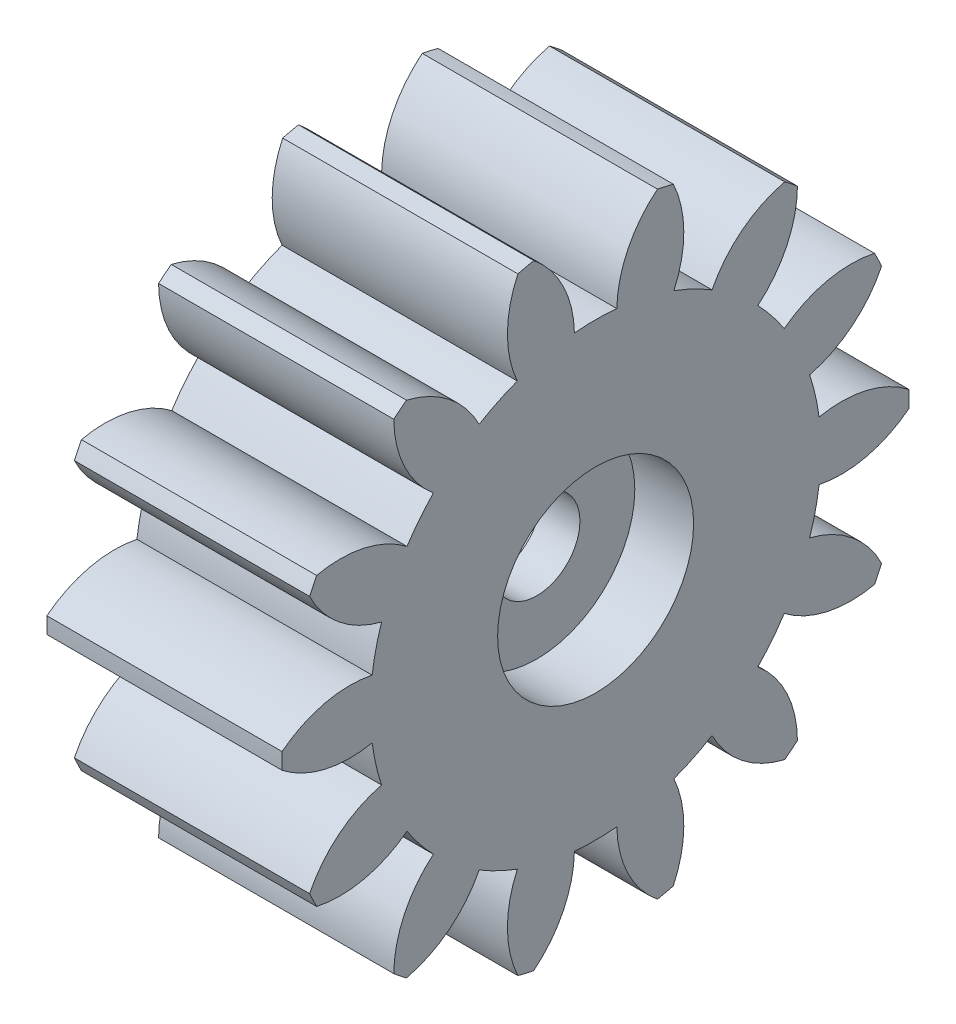
SolidWorks part; units mm, degrees
ref_plane "Plane1" through (0, 0, 0) normal (0, 0, 1) x (1, 0, 0)
ref_plane "Plane2" through (0, 0, 0) normal (0, 1, 0) x (1, 0, 0)
ref_plane "Plane3" through (0, 0, 0) normal (1, 0, 0) x (0, 0, -1)
other "Configuration Table"
sketch "HoldingSke" plane through (0, 0, 0) normal (0, 1, 0) x (1, 0, 0)
  line L0 (0, 0) -> (0.9703, -0.2419)
  line L1 (-15, 0) -> (100, 0) construction
  line L2 (0, 0) -> (-2.1039, 2.3779)
  line L3 (0, 0) -> (-11.863, 4.5341)
  line L4 (0, 0) -> (8.3795, 2.0892)
  line L5 (0, 0) -> (-46.8476, -17.4728)
  line L6 (0, 0) -> (-4.9738, -3.3558)
  line L7 (-2.1039, 2.3779) -> (8.6586, 51.2059)
  line L8 (-76.2, 54.61) -> (-75.3, 54.61)
  line L9 (-71.009, 38.7566) -> (-53.1078, 45.2721)
  line L10 (-76.2, 71.12) -> (104.1128, 71.12)
  line L11 (0, 0) -> (-6, 0)
  line L12 (-76.2, 101.6) -> (-76.162, 101.6)
  line L13 (24.9733, 27.94) -> (52.9518, 28.4284)
  line L14 (24.9733, 27.94) -> (24.9743, 27.94)
  line L15 (24.9733, 27.94) -> (100.4006, 29.5858)
  line L16 (-63.627, -1) -> (-12.827, -1)
  circle A0 centre (0, 0) radius 2.5
  circle A1 centre (0, 0) radius 5.749
  circle A2 centre (0, 0) radius 37.5
  circle A3 centre (0, 0) radius 2.5
  dimension "MHD" = 11.498
  dimension "Hub_dia" = 75
  dimension "Bore" = 5
  dimension "MBD" = 5
  dimension "Num_teeth" = 14
  dimension "Pitch" = 1
  dimension "Overall_len" = 50
  dimension "Show_teeth" = 14
  dimension "Thickness" = 6
  dimension "OAL" = 50.0001
  dimension "T_dim" = 0.9
  dimension "Ap" = 20
  dimension "H" = 19.05
  dimension "Pitch_radius" = 180.3128
  dimension "Width" = 6
  dimension "Backlash" = 0.038
  dimension "Addendum_fac" = 1
  dimension "Dedendum_fac" = 1.25
  dimension "Clearance_fac" = 0.25
  dimension "Dedendum_add" = 0.001
  dimension "Module" = 1
sketch "BasProSke" plane through (0, 0, 0) normal (0, 1, 0) x (1, 0, 0)
  line L0 (-10, 0) -> (60, 0) construction
  line L1 (0, 0) -> (0, 8)
  line L2 (0, 0) -> (6, 0)
  line L3 (6, 0) -> (6, 8)
  line L4 (6, 8) -> (0, 8)
  dimension "Thickness" = 6
  dimension "Diameter" = 16
revolve "Base-Revolve" add sketch "BasProSke" angle 360 about L0
sketch "TooCutSke" plane through (0, 0, 0) normal (1, 0, 0) x (0, 0, -1)
  line L1 (0, 0) -> (0, 107) construction
  line L2 (0, 0) -> (-0.8502, 6.9482) construction
  line L3 (0, 0) -> (-3.0989, 13.5772) construction
  line L4 (-0.8502, 6.9482) -> (-1.5494, 6.7886) construction
  arc A0 (0.5404, 5.7235) -> (-0.5404, 5.7235) centre (0, 0) ccw
  arc A1 (1.6036, 7.8636) -> (-1.6036, 7.8636) centre (0, 0) ccw
  circle A2 centre (0, 0) radius 7 construction
  circle A3 centre (0, 0) radius 6.5778 construction
  arc A4 (-0.5404, 5.7235) -> (-1.6036, 7.8636) centre (-3.3398, 5.6669) ccw
  arc A5 (1.6036, 7.8636) -> (0.5404, 5.7235) centre (3.3398, 5.6669) ccw
  dimension "Root_dia" = 11.498
  dimension "Overcut_dia" = 16.0508
  dimension "Pitch_dia" = 14
  dimension "Base_dia" = 13.1557
  dimension "Flank_rad" = 2.8
  dimension "Half_ang" = 12.857
  dimension "Half_CT" = 0.7173
extrude "ToothCut" cut sketch "TooCutSke" along normal through all
fillet "Breaks" [suppressed] radius 0.02
fillet "RootFillets" [suppressed] radius 0.251
pattern_circular "TeethCuts" count 14 every 25.714 about axis through (-10, 0, 0) along (1, 0, 0) of "ToothCut", "RootFillets", "Breaks"
sketch "HubNeaOneSke" plane through (0, 0, 0) normal (-1, 0, 0) x (0, 0, 1)
  circle A0 centre (0, 0) radius 5.749
  dimension "Diameter" = 11.498
extrude "HubNearOne" [suppressed] add sketch "HubNeaOneSke" along normal blind 44.0001
sketch "HubNeaBotSke" plane through (0, 0, 0) normal (-1, 0, 0) x (0, 0, 1)
  circle A0 centre (0, 0) radius 5.749
  dimension "Diameter" = 11.498
extrude "HubNearBoth" [suppressed] add sketch "HubNeaBotSke" along normal blind 22
ref_plane "FarPln" through (6, 0, 0) normal (1, 0, 0) x (0, 0, -1)
sketch "HubFarSke" plane through (6, 0, 0) normal (1, 0, 0) x (0, 0, -1)
  circle A0 centre (0, 0) radius 5.749
  dimension "Diameter" = 11.498
extrude "HubFar" [suppressed] add sketch "HubFarSke" along normal blind 22
sketch "BorSke" plane through (0, 0, 0) normal (1, 0, 0) x (0, 0, -1)
  circle A0 centre (0, 0) radius 2.5
  dimension "Diameter" = 5
extrude "Bore" cut sketch "BorSke" along normal mid plane 100.0001
sketch "KeySke" plane through (0, 0, 0) normal (1, 0, 0) x (0, 0, -1)
  line L0 (-1, 0) -> (-1, 3.4)
  line L1 (-1, 3.4) -> (1, 3.4)
  line L2 (1, 3.4) -> (1, 0)
  line L3 (0, 0) -> (0, 34) construction
  line L4 (-1, 0) -> (1, 0)
  dimension "Offset" = 3.4
  dimension "Width" = 2
extrude "Keyway" [suppressed] cut sketch "KeySke" along normal mid plane 100.0001
pattern_circular "Keyway2" [suppressed] count 2 every 90 about axis through (-10, 0, 0) along (1, 0, 0)
sketch "Sketch1" plane through (6, 0, 0) normal (1, 0, 0) x (0, 0, -1)
  circle A0 centre (0, 0) radius 2.5
  circle A1 centre (0, 0) radius 2.5 construction
extrude "Boss-Extrude1" add sketch "Sketch1" against normal blind 2.5
sketch "Sketch2" plane through (6, 0, 0) normal (1, 0, 0) x (0, 0, -1)
  circle A0 centre (0, 0) radius 2.5
  circle A1 centre (0, 0) radius 2.5 construction
extrude "Cut-Extrude1" cut sketch "Sketch2" against normal blind 1.5
sketch "Sketch3" plane through (4.5, 0, 0) normal (1, 0, 0) x (0, 0, -1)
  circle A0 centre (0, 0) radius 1.1
  dimension "D1" = 2.2
extrude "Cut-Extrude2" cut sketch "Sketch3" against normal through all
equation "' \"Module@HoldingSke\" = 6.35"
equation "' \"Num_teeth@HoldingSke\" = 12"
equation "' \"Ap@HoldingSke\" =  20"
equation "' \"Ap@HoldingSke\" = 20"
equation "' \"Width@HoldingSke\" = 0.5 * 25.4"
equation "' \"Hub_dia@HoldingSke\"= 1 * 25.4"
equation "' \"Hub_dia@HoldingSke\" = 1 * 25.4"
equation "' \"Overall_len@HoldingSke\" = 1.0 * 25.4"
equation "' \"Bore@HoldingSke\" = 0.75 * 25.4"
equation "' \"T_dim@HoldingSke\" = 0.1 * 25.4"
equation "' \"Width@KeySke\" = 0.25 * 25.4"
equation "' \"Show_teeth@HoldingSke\" = 13"
equation "' \"Backlash@HoldingSke\" = 0.009 * 25.4"
equation "' \"Addendum_fac@HoldingSke\" = 1.0"
equation "' \"Dedendum_fac@HoldingSke\" = 1.25"
equation "' \"Dedendum_add@HoldingSke\" = 0.00005 * 25.4"
equation "' \"Clearance_fac@HoldingSke\" = 0.25"
equation "\"Pitch@HoldingSke\" = 1 / \"Module@HoldingSke\""
equation "\"Overcut_dia@TooCutSke\" = (\"Num_teeth@HoldingSke\" + 2 * \"Addendum_fac@HoldingSke\") / \"Pitch@HoldingSke\" + 0.002 * 25.4"
equation "\"Pitch_dia@TooCutSke\" = \"Num_teeth@HoldingSke\" / \"Pitch@HoldingSke\""
equation "\"Base_dia@TooCutSke\" = \"Num_teeth@HoldingSke\" / \"Pitch@HoldingSke\" * cos((\"Ap@HoldingSke\"  * 3.14159265 / 180))"
equation "\"Root_dia@TooCutSke\" = (\"Num_teeth@HoldingSke\" + 2) / \"Pitch@HoldingSke\" - 2 * (\"Addendum_fac@HoldingSke\" + \"Dedendum_fac@HoldingSke\") / \"Pitch@HoldingSke\" - \"Dedendum_add@HoldingSke\" * 2"
equation "\"Half_ang@TooCutSke\" = 180 / \"Num_teeth@HoldingSke\""
equation "\"Half_CT@TooCutSke\" = \"Num_teeth@HoldingSke\" / \"Pitch@HoldingSke\" * sin((3.14159265 / 2 / \"Num_teeth@HoldingSke\")) / 2 - 7 * \"Backlash@HoldingSke\" / 4"
equation "\"Flank_rad@TooCutSke\" = \"Num_teeth@HoldingSke\" / \"Pitch@HoldingSke\" / 5"
equation "\"Radius@RootFillets\" = \"Clearance_fac@HoldingSke\" / \"Pitch@HoldingSke\" + \"Dedendum_add@HoldingSke\""
equation "\"Break_rad@Breaks\" = 0.02 / \"Pitch@HoldingSke\""
equation "\"Thickness@HoldingSke\" = \"Width@HoldingSke\""
equation "\"OAL@HoldingSke\" = \"Thickness@HoldingSke\""
equation "\"MHD@HoldingSke\" = (\"Num_teeth@HoldingSke\" + 2) / \"Pitch@HoldingSke\" - 2 * (\"Addendum_fac@HoldingSke\" + \"Dedendum_fac@HoldingSke\")  / \"Pitch@HoldingSke\" - \"Dedendum_add@HoldingSke\" * 2"
equation "\"MBD@HoldingSke\" = (\"Num_teeth@HoldingSke\" + 2) / \"Pitch@HoldingSke\" - 2 * (\"Addendum_fac@HoldingSke\" + \"Dedendum_fac@HoldingSke\")  / \"Pitch@HoldingSke\" - \"Dedendum_add@HoldingSke\" * 2 - 0.002 * 25.4"
equation "\"MHD@HoldingSke\" = ((sgn( \"MHD@HoldingSke\" - \"Hub_dia@HoldingSke\" )-1)*( \"MHD@HoldingSke\" - \"Hub_dia@HoldingSke\" ))/-2+ \"Hub_dia@HoldingSke\""
equation "\"MBD@HoldingSke\" = ((sgn( \"MBD@HoldingSke\" - \"Bore@HoldingSke\" )-1)*( \"MBD@HoldingSke\" - \"Bore@HoldingSke\" ))/-2+ \"Bore@HoldingSke\""
equation "\"OAL@HoldingSke\" = ((sgn( \"OAL@HoldingSke\" - \"Overall_len@HoldingSke\" )+1)*( \"OAL@HoldingSke\" - \"Overall_len@HoldingSke\" ))/2 + \"Overall_len@HoldingSke\" + 0.000002 * 25.4"
equation "\"Num_teeth@TeethCuts\" = int( \"Show_teeth@HoldingSke\" ) + 1"
equation "\"Num_teeth@TeethCuts\" = ((sgn( \"Num_teeth@TeethCuts\" - \"Num_teeth@HoldingSke\" )-1)*( \"Num_teeth@TeethCuts\" - \"Num_teeth@HoldingSke\" ))/-2+ \"Num_teeth@HoldingSke\""
equation "\"Num_teeth@TeethCuts\" = ((sgn( \"Num_teeth@TeethCuts\" - 2.0)+1)*( \"Num_teeth@TeethCuts\" - 2.0))/2 +2.0"
equation "\"Angle@TeethCuts\" = 360.0 / \"Num_teeth@HoldingSke\""
equation "\"Diameter@BasProSke\" = (\"Num_teeth@HoldingSke\" + 2 * \"Addendum_fac@HoldingSke\") / \"Pitch@HoldingSke\""
equation "\"Thickness@BasProSke\"  = \"Thickness@HoldingSke\""
equation "' \"Fillet_rad@BasProSke\" =  \"Thickness@HoldingSke\" * 0.05"
equation "' \"Fillet_rad@BasProSke\" = \"Thickness@HoldingSke\" * 0.05"
equation "\"MHD@HoldingSke\" = ((sgn( \"MHD@HoldingSke\" - \"Root_dia@TooCutSke\" )-1)*( \"MHD@HoldingSke\" - \"Root_dia@TooCutSke\" ))/-2+ \"Root_dia@TooCutSke\""
equation "\"Diameter@HubNeaOneSke\" = \"MHD@HoldingSke\""
equation "\"Length@HubNearOne\" = \"OAL@HoldingSke\" - \"Thickness@BasProSke\""
equation "\"Diameter@HubNeaBotSke\" = \"MHD@HoldingSke\""
equation "\"Length@HubNearBoth\" = ( \"OAL@HoldingSke\" - \"Thickness@BasProSke\" ) / 2.0"
equation "\"Thickness@FarPln\" = \"Thickness@BasProSke\""
equation "\"Diameter@HubFarSke\" = \"MHD@HoldingSke\""
equation "\"Length@HubFar\" = ( \"OAL@HoldingSke\" - \"Thickness@BasProSke\" ) / 2.0"
equation "\"Diameter@BorSke\" = \"MBD@HoldingSke\""
equation "\"D1@Bore\" = \"OAL@HoldingSke\" * 2.0"
equation "\"D1@Keyway\" = \"OAL@HoldingSke\" * 2.0"
equation "\"Offset@KeySke\" = \"T_dim@HoldingSke\" + \"MBD@HoldingSke\" / 2.0"
